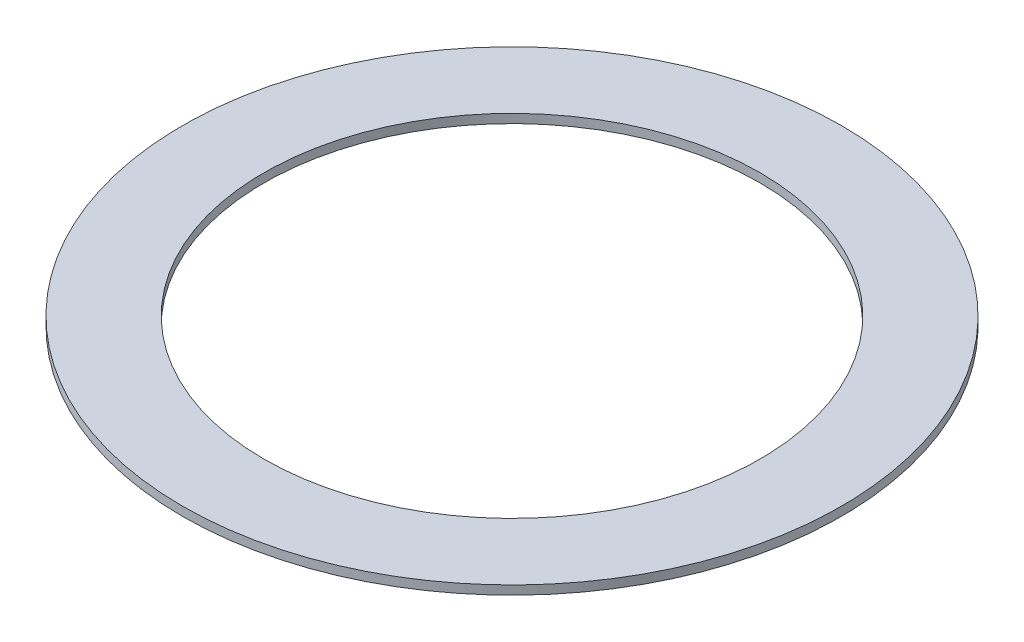
SolidWorks part; units mm, degrees
ref_plane "Front Plane" through (0, 0, 0) normal (0, 0, 1) x (1, 0, 0)
ref_plane "Top Plane" through (0, 0, 0) normal (0, 1, 0) x (1, 0, 0)
ref_plane "Right Plane" through (0, 0, 0) normal (1, 0, 0) x (0, 0, -1)
sketch "Sketch1" plane through (0, 0, 0) normal (0, 1, 0) x (1, 0, 0)
  circle A0 centre (0, 0) radius 88.9
  circle A1 centre (0, 0) radius 118.11
  dimension "D1" = 177.8
  dimension "D2" = 236.22
extrude "Boss-Extrude1" add sketch "Sketch1" along normal blind 3.175
equation "\"2x3.5\"=3.60815"
